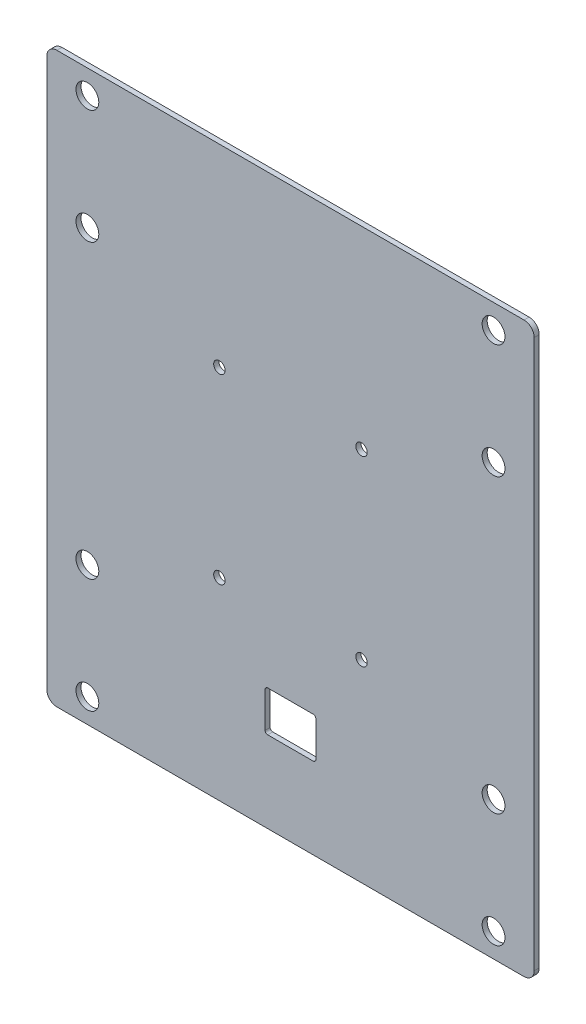
SolidWorks part; units mm, degrees
material "PE High Density"
ref_plane "Front Plane" through (0, 0, 0) normal (0, 0, 1) x (1, 0, 0)
ref_plane "Top Plane" through (0, 0, 0) normal (0, 1, 0) x (1, 0, 0)
ref_plane "Right Plane" through (0, 0, 0) normal (1, 0, 0) x (0, 0, -1)
sketch "Sketch1" plane through (0, 0, 0) normal (0, 0, 1) x (1, 0, 0)
  line L1 (-152.4, 177.8) -> (152.4, 177.8)
  line L2 (-152.4, 177.8) -> (-152.4, -177.8)
  line L3 (-152.4, -177.8) -> (152.4, -177.8)
  line L4 (152.4, 177.8) -> (152.4, -177.8)
  line L5 (-152.4, 177.8) -> (152.4, -177.8) construction
  line L6 (-152.4, -177.8) -> (152.4, 177.8) construction
  point P0 (0, 0)
  dimension "D1" = 304.8
  dimension "D2" = 355.6
extrude "Boss-Extrude1" add sketch "Sketch1" along normal blind 3.175
sketch "Sketch2" plane through (0, 0, 3.175) normal (0, 0, 1) x (1, 0, 0)
  line L0 (-127, -91.2813) -> (127, -91.2813) construction
  line L1 (127, 162.7187) -> (-127, 162.7187)
  line L2 (127, 162.7187) -> (127, -162.7187)
  line L3 (127, -162.7187) -> (-127, -162.7188)
  line L4 (-127, 162.7187) -> (-127, -162.7188)
  line L5 (127, 162.7187) -> (-127, -162.7188) construction
  line L6 (127, -162.7187) -> (-127, 162.7187) construction
  line L7 (-152.4, 177.8) -> (-152.4, -177.8) construction
  line L8 (-127, 91.2812) -> (127, 91.2812) construction
  line L10 (0, 162.7187) -> (0, 91.2812) construction
  line L11 (0, 91.2812) -> (0, 0) construction
  line L12 (0, 0) -> (0, -91.2812) construction
  line L13 (0, -91.2812) -> (0, -162.7188) construction
  line L14 (15.875, 101.6) -> (-15.875, 101.6)
  line L15 (15.875, 101.6) -> (15.875, -101.6)
  line L16 (15.875, -101.6) -> (-15.875, -101.6)
  line L17 (-15.875, 101.6) -> (-15.875, -101.6)
  line L18 (15.875, -101.6) -> (-15.875, -101.6)
  line L19 (15.875, -101.6) -> (15.875, -127)
  line L20 (15.875, -127) -> (-15.875, -127)
  line L21 (-15.875, -101.6) -> (-15.875, -127)
  point P0 (0, 0)
  point P17 (0, -127)
  point P22 (0, 101.6)
  point P25 (-15.875, 0)
  dimension "D1" = 25.4
  dimension "D2" = 71.4375
  dimension "D3" = 127
  dimension "D4" = 203.2
  dimension "D5" = 31.75
  dimension "D6" = 25.4
hole_wizard "9/16 (0.5625) Diameter Hole1" positions "Sketch3" profile "Sketch4" hole size "9/16" standard "ANSI Inch" end condition through all
sketch "Sketch3" plane through (0, 0, 3.175) normal (0, 0, 1) x (1, 0, 0)
  point P0 (-127, 162.7187)
  point P3 (-127, 91.2812)
  point P6 (-127, -91.2813)
  point P9 (-127, -162.7188)
  point P12 (127, -162.7187)
  point P15 (127, -91.2813)
  point P18 (127, 91.2812)
  point P21 (127, 162.7187)
sketch "Sketch4" plane through (-127, 162.7187, 3.175) normal (1, 0, 0) x (0, -1, 0)
  line L0 (0, 0) -> (0, 3.175)
  line L1 (0, 3.175) -> (7.1437, 3.175)
  line L2 (7.1437, 3.175) -> (7.1437, 0)
  line L5 (7.1437, 0) -> (0, 0)
  line L11 (0, -6.35) -> (0, 107.95) construction
  dimension "Thru Hole Dia." = 14.2875
  dimension "Thru Hole Depth" = 3.175
fillet "Fillet1" radius 6.35 4 edges at (152.4, -177.8, 1.5875) (-152.4, -177.8, 1.5875) (152.4, 177.8, 1.5875) (-152.4, 177.8, 1.5875)
sketch "Sketch7" plane through (0, 0, 0) normal (0, 0, -1) x (-1, 0, 0)
  line L0 (-127, -162.7187) -> (127, 162.7187) construction
  line L1 (44.45, 56.9516) -> (-44.45, 56.9516)
  line L2 (44.45, 56.9516) -> (44.45, -56.9516)
  line L3 (44.45, -56.9516) -> (-44.45, -56.9516)
  line L4 (-44.45, 56.9516) -> (-44.45, -56.9516)
  line L5 (44.45, 56.9516) -> (-44.45, -56.9516) construction
  line L6 (44.45, -56.9516) -> (-44.45, 56.9516) construction
  point P0 (0, 0)
  dimension "D1" = 88.9
hole_wizard "1/4 Clearance Hole1" positions "Sketch8" profile "Sketch9" hole size "1/4" standard "ANSI Inch" end condition through all
sketch "Sketch8" plane through (0, 0, 0) normal (0, 0, -1) x (-1, 0, 0)
  point P0 (-44.45, 56.9516)
  point P3 (-44.45, -56.9516)
  point P6 (44.45, 56.9516)
  point P9 (44.45, -56.9516)
sketch "Sketch9" plane through (44.45, 56.9516, 0) normal (1, 0, 0) x (0, 1, 0)
  line L0 (0, 0) -> (0, 3.175)
  line L1 (0, 3.175) -> (3.5712, 3.175)
  line L2 (3.5712, 3.175) -> (3.5712, 0)
  line L5 (3.5712, 0) -> (0, 0)
  line L11 (0, -6.35) -> (0, 107.95) construction
  dimension "Thru Hole Dia." = 7.1425
  dimension "Thru Hole Depth" = 3.175
extrude "Cut-Extrude1" cut sketch "Sketch2" against normal through all contours L16 L21 L20 L19
sketch "Sketch10" plane through (0, 0, 0) normal (0, 0, -1) x (-1, 0, 0)
  line L0 (-146.05, 177.8) -> (146.05, 177.8) construction
  line L1 (12.7, 101.6) -> (-12.7, 101.6)
  line L2 (12.7, 101.6) -> (12.7, -82.55)
  line L3 (12.7, -82.55) -> (-12.7, -82.55)
  line L4 (-12.7, 101.6) -> (-12.7, -82.55)
  point P6 (0, -82.55)
  dimension "D1" = 25.4
  dimension "D2" = 184.15
  dimension "D3" = 76.2
fillet "Fillet2" radius 1.5875 4 edges at (15.875, -127, 1.5875) (-15.875, -127, 1.5875) (-15.875, -101.6, 1.5875) (15.875, -101.6, 1.5875)
